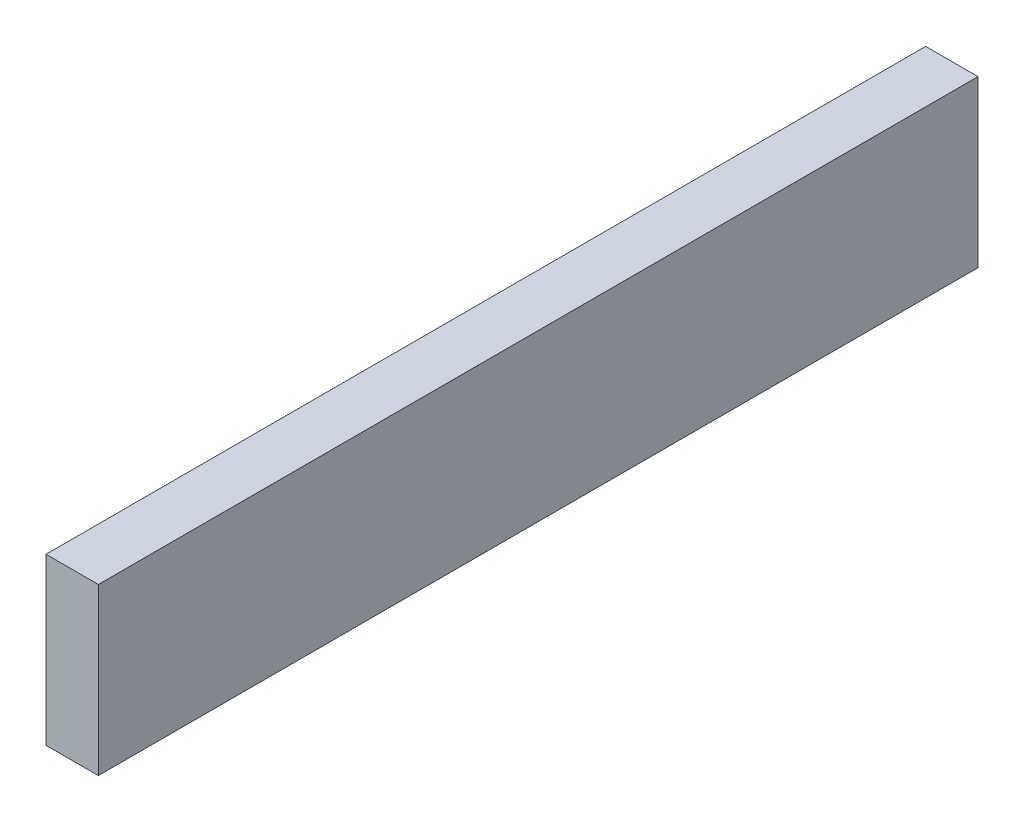
SolidWorks part; units mm, degrees
ref_plane "Front Plane" through (0, 0, 0) normal (0, 0, 1) x (1, 0, 0)
ref_plane "Top Plane" through (0, 0, 0) normal (0, 1, 0) x (1, 0, 0)
ref_plane "Right Plane" through (0, 0, 0) normal (1, 0, 0) x (0, 0, -1)
sketch "Sketch1" plane through (0, 0, 0) normal (1, 0, 0) x (0, 0, -1)
  line L1 (-40.5481, 4.7422) -> (9.8577, 4.7422)
  line L2 (-40.5481, 4.7422) -> (-40.5481, -4.7422)
  line L3 (-40.5481, -4.7422) -> (9.8577, -4.7422)
  line L4 (9.8577, 4.7422) -> (9.8577, -4.7422)
  point P0 (0, 0)
  point P6 (-10.236, 4.7463)
  point P7 (0, 0)
  point P8 (0, 0)
  point P10 (0, 0)
extrude "Boss-Extrude1" add sketch "Sketch1" along normal blind 3
